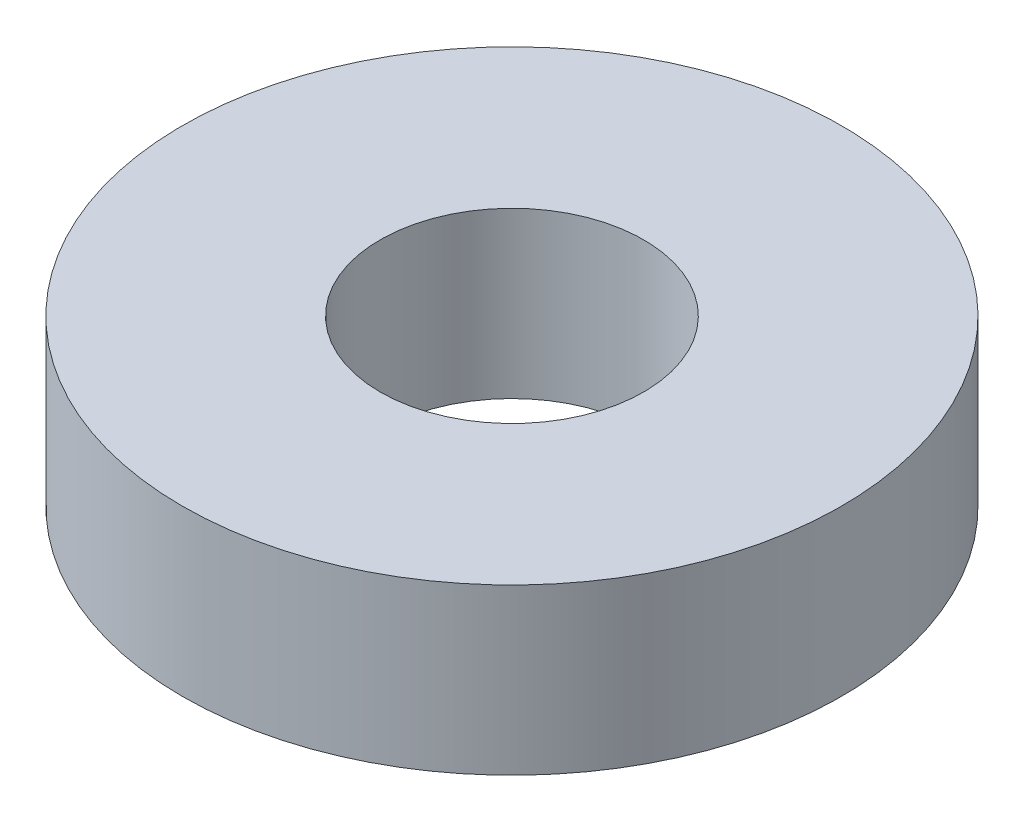
SolidWorks part; units mm, degrees
ref_plane "Front Plane" through (0, 0, 0) normal (0, 0, 1) x (1, 0, 0)
ref_plane "Top Plane" through (0, 0, 0) normal (0, 1, 0) x (1, 0, 0)
ref_plane "Right Plane" through (0, 0, 0) normal (1, 0, 0) x (0, 0, -1)
sketch "Sketch1" plane through (0, 0, 0) normal (0, 1, 0) x (1, 0, 0)
  circle A0 centre (0, 0) radius 4
  circle A1 centre (0, 0) radius 10
  dimension "D1" = 8
  dimension "D2" = 20
extrude "Boss-Extrude1" add sketch "Sketch1" along normal blind 5
